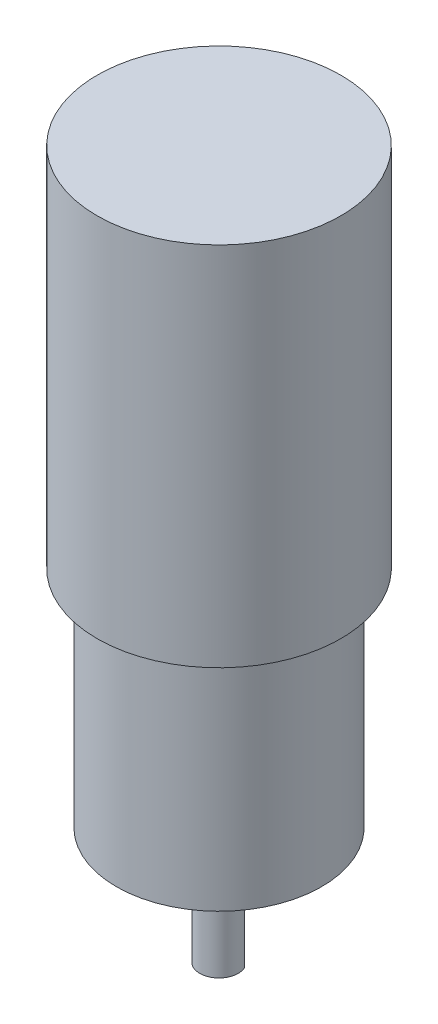
SolidWorks part; units mm, degrees
ref_plane "Front Plane" through (0, 0, 0) normal (0, 0, 1) x (1, 0, 0)
ref_plane "Top Plane" through (0, 0, 0) normal (0, 1, 0) x (1, 0, 0)
ref_plane "Right Plane" through (0, 0, 0) normal (1, 0, 0) x (0, 0, -1)
sketch "Sketch2" plane through (0, 0, 0) normal (0, 1, 0) x (1, 0, 0)
  line L0 (-2.75, 1.199) -> (2.75, 1.199)
  circle A0 centre (0, 0) radius 3
  dimension "D1" = 6
  dimension "D2" = 5.5
extrude "Boss-Extrude1" add sketch "Sketch2" along normal blind 12 contours L0 A0
sketch "Sketch3" plane through (0, 12, 0) normal (0, 1, 0) x (1, 0, 0)
  arc A0 (-2.75, 1.199) -> (2.75, 1.199) centre (0, 0) ccw construction
  arc A1 (-2.75, 1.199) -> (2.75, 1.199) centre (0, 0) ccw
  circle A2 centre (0, 0) radius 3
  line M1 (2.75, 1.199) -> (-2.75, 1.199)
  arc M2 (-2.75, 1.199) -> (2.75, 1.199) centre (0, 0) ccw
extrude "Boss-Extrude2" add sketch "Sketch3" along normal blind 3.2 contours A2 M1 | M2 M1
sketch "Sketch5" plane through (0, 15.2, 0) normal (0, 1, 0) x (1, 0, 0)
  line L0 (-9, 4.3589) -> (-9, -4.3589)
  line L1 (9, 4.3589) -> (9, -4.3589)
  arc A0 (-9, -4.3589) -> (9, -4.3589) centre (0, 0) ccw
  arc A1 (9, 4.3589) -> (-9, 4.3589) centre (0, 0) ccw
  dimension "D1" = 20
  dimension "D2" = 18
extrude "Boss-Extrude3" add sketch "Sketch5" along normal blind 3
sketch "Sketch6" plane through (0, 18.2, 0) normal (0, 1, 0) x (1, 0, 0)
  circle A0 centre (0, 0) radius 16
  dimension "D1" = 32
extrude "Boss-Extrude4" add sketch "Sketch6" along normal blind 35
sketch "Sketch7" plane through (0, 53.2, 0) normal (0, 1, 0) x (1, 0, 0)
  circle A0 centre (0, 0) radius 19
  dimension "D1" = 38
extrude "Boss-Extrude5" add sketch "Sketch7" along normal blind 57.1
sketch "Sketch8" plane through (0, 18.2, 0) normal (0, -1, 0) x (1, 0, 0)
  circle A0 centre (0, 0) radius 13 construction
  circle A1 centre (0, 13) radius 1.5
  circle A2 centre (13, 0) radius 1.5
  circle A3 centre (0, -13) radius 1.5
  circle A4 centre (-13, 0) radius 1.5
  point P14 (0, 0)
  dimension "D1" = 26
  dimension "D2" = 3
  dimension "D3" = 4
extrude "Cut-Extrude1" cut sketch "Sketch8" against normal blind 10
